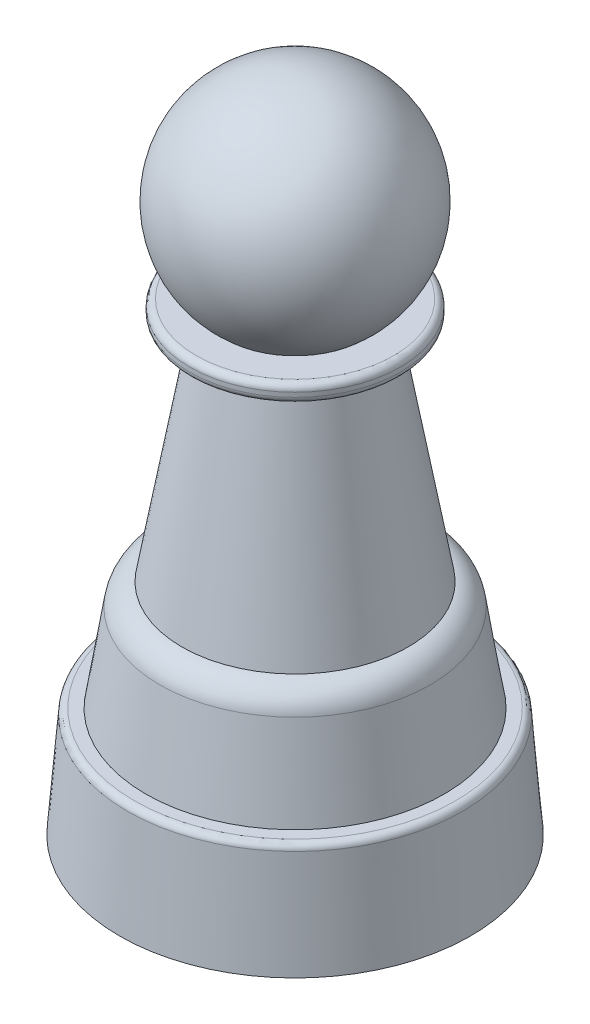
SolidWorks part; units mm, degrees
ref_plane "Front Plane" through (0, 0, 0) normal (0, 0, 1) x (1, 0, 0)
ref_plane "Top Plane" through (0, 0, 0) normal (0, 1, 0) x (1, 0, 0)
ref_plane "Right Plane" through (0, 0, 0) normal (1, 0, 0) x (0, 0, -1)
sketch "Sketch3" plane through (0, 0, 0) normal (1, 0, 0) x (0, 0, -1)
  line L0 (0, 44.3007) -> (0, 19.3007)
  line L1 (0, 63.9052) -> (0, -37.4735) construction
  line L2 (8.3294, 20.1767) -> (12.8982, -5.7342)
  line L3 (17.3002, -30.6993) -> (0, -30.6993)
  line L4 (0, -30.6993) -> (0, 44.3007)
  line L5 (0, 44.3007) -> (0, -30.6993)
  line L6 (7.9768, 22.1767) -> (11.25, 22.1767)
  line L7 (0, 22.1767) -> (0, 20.1767)
  line L8 (8.3294, 20.1767) -> (11.25, 20.1767)
  line L9 (12, 21.4267) -> (12, 20.9267)
  line L10 (-23.1126, -18.1993) -> (0, -18.1993)
  line L11 (15.4042, -8.2253) -> (17, -18.1993)
  line L12 (0, -30.6993) -> (20, -30.6993)
  line L13 (17, -18.1993) -> (18.3076, -18.1993)
  line L14 (19.0552, -18.8895) -> (20, -30.6993)
  arc A0 (7.9768, 22.1767) -> (0, 44.3007) centre (0, 31.8007) ccw
  arc A1 (11.25, 20.1767) -> (12, 20.9267) centre (11.25, 20.9267) ccw
  arc A2 (11.25, 22.1767) -> (12, 21.4267) centre (11.25, 21.4267) cw
  arc A3 (15.4042, -8.2253) -> (12.4418, -5.6993) centre (12.4418, -8.6993) ccw
  arc A4 (18.3076, -18.1993) -> (19.0552, -18.8895) centre (18.3076, -18.9493) cw
  point P15 (12, 20.1767)
  point P18 (12, 22.1767)
  point P25 (15, -5.6993)
  point P32 (19, -18.1993)
  dimension "D1" = 25
  dimension "D5" = 0.75
  dimension "D11" = 3
  dimension "D7" = 0.75
  dimension "D2" = 10
  dimension "D3" = 2
  dimension "D4" = 12
  dimension "D6" = 75
  dimension "D8" = 12.5
  dimension "D10" = 17
  dimension "D12" = 20
  dimension "D13" = 2
revolve "Revolve3" add sketch "Sketch3" angle 360 about L1
